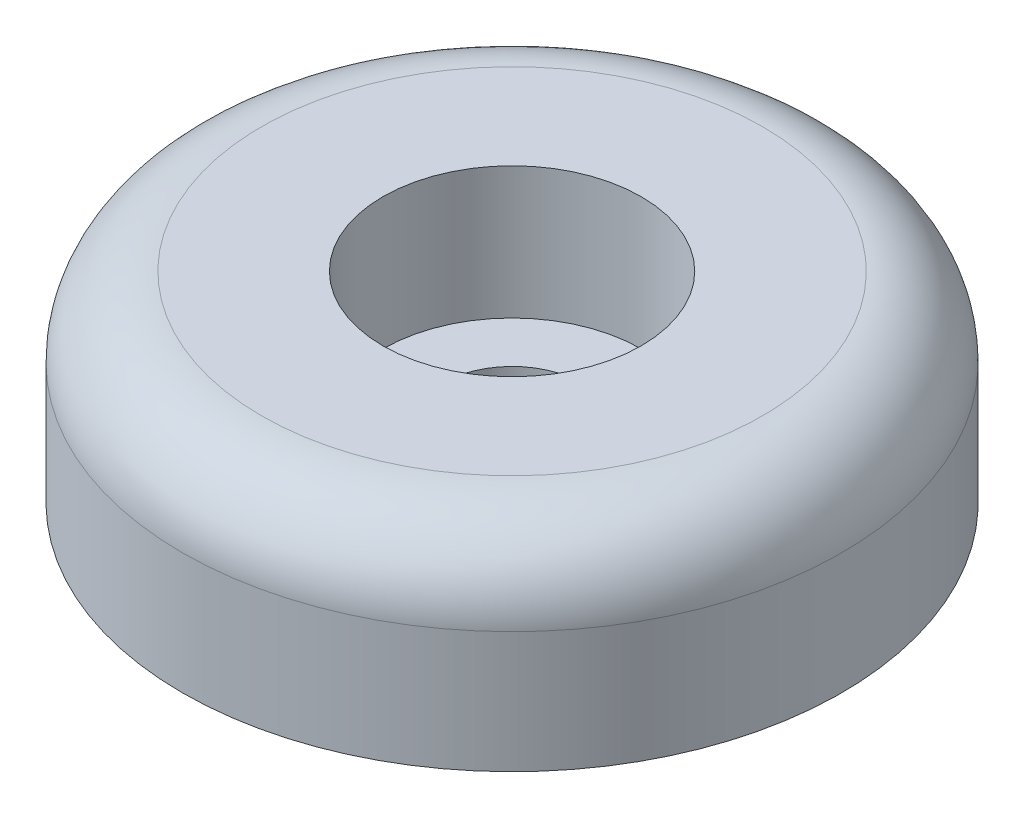
SolidWorks part; units mm, degrees
ref_plane "Plan de face" through (0, 0, 0) normal (0, 0, 1) x (1, 0, 0)
ref_plane "Plan de dessus" through (0, 0, 0) normal (0, 1, 0) x (1, 0, 0)
ref_plane "Plan de droite" through (0, 0, 0) normal (1, 0, 0) x (0, 0, -1)
sketch "Esquisse1" plane through (0, 0, 0) normal (0, 0, 1) x (1, 0, 0)
  line L0 (-29.3001, 0) -> (34.1431, 0) construction
  line L1 (0, 17.6756) -> (0, -19.8633) construction
  line L2 (-2.65, 0) -> (-12.5, 0)
  line L3 (-12.5, 0) -> (-12.5, 7.6)
  line L4 (-12.5, 7.6) -> (-4.9, 7.6)
  line L5 (-4.9, 7.6) -> (-4.9, 2.6)
  line L6 (-4.9, 2.6) -> (-2.65, 2.6)
  line L7 (-2.65, 2.6) -> (-2.65, 0)
  dimension "D1" = 2.65
  dimension "D2" = 4.9
  dimension "D3" = 7.6
  dimension "D4" = 5
  dimension "D5" = 12.5
revolve "Révolution1" add sketch "Esquisse1" angle 360 about L1
fillet "Congé1" radius 3 1 edges at (0, 7.6, 12.5)
